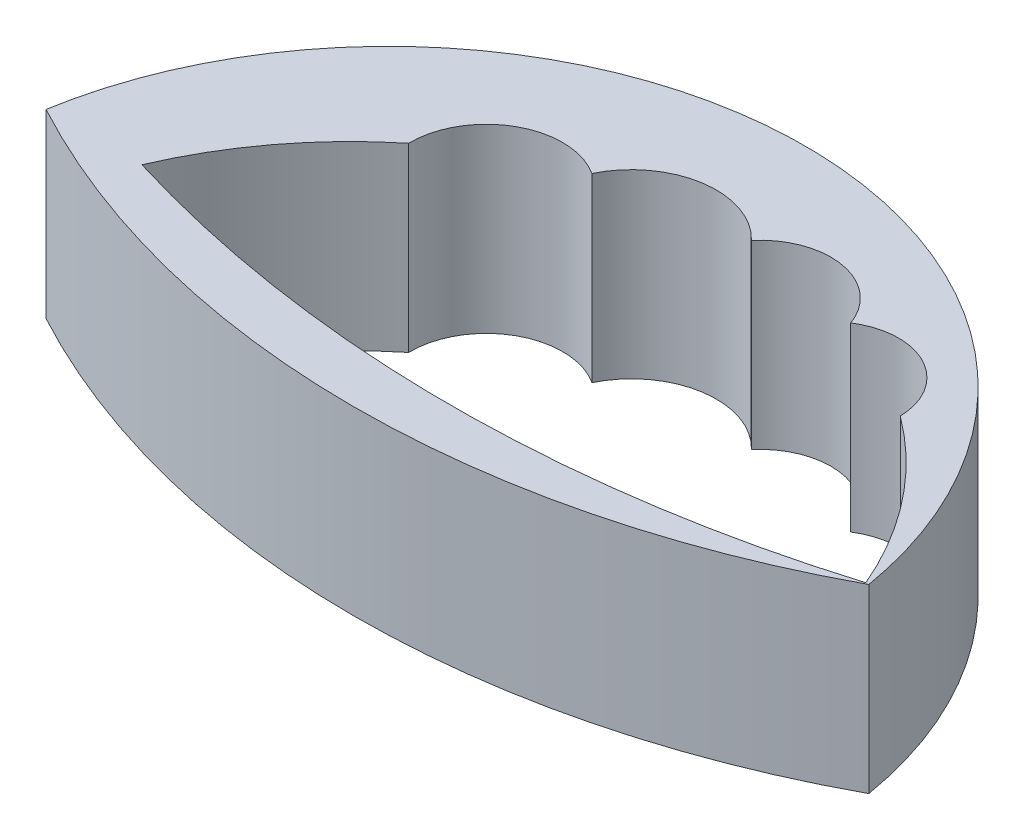
SolidWorks part; units mm, degrees
material "PP Copolymer"
ref_plane "Front Plane" through (0, 0, 0) normal (0, 0, 1) x (1, 0, 0)
ref_plane "Top Plane" through (0, 0, 0) normal (0, 1, 0) x (1, 0, 0)
ref_plane "Right Plane" through (0, 0, 0) normal (1, 0, 0) x (0, 0, -1)
sketch "Sketch1" plane through (0, 0, 0) normal (0, 1, 0) x (1, 0, 0)
  arc A2 (0, 0) -> (55.8747, 0) centre (27.9373, -4.7075) cw
  arc A3 (0, 0) -> (55.8747, 0) centre (27.9373, 51.9169) ccw
  point P4 (0, 0)
  point P5 (0, 0)
  point P7 (0, 0)
  point P8 (55.8747, 0)
extrude "Boss-Extrude1" add sketch "Sketch1" along normal blind 12.3
sketch "Sketch2" plane through (0, 12.3, 0) normal (0, 1, 0) x (1, 0, 0)
  arc A0 (6.5129, 0) -> (14.3047, 10.3192) centre (31.0915, -10.4575) cw
  arc A1 (6.5129, 0) -> (55.6701, 0) centre (31.0915, 80.7353) ccw
  arc A2 (14.3047, 10.3192) -> (22.3051, 14.7668) centre (19.488, 10.4148) cw
  arc A3 (22.3051, 14.7668) -> (31.6568, 16.2473) centre (27.4946, 12.2624) cw
  arc A4 (31.6568, 16.2473) -> (39.8779, 14.7668) centre (35.3424, 13.1474) cw
  arc A5 (39.8779, 14.7668) -> (47.0372, 10.9715) centre (42.3926, 10.8603) cw
  arc A6 (47.0372, 10.9715) -> (55.6701, 0) centre (31.0915, -10.4575) cw
extrude "Cut-Extrude1" cut sketch "Sketch2" against normal through all
